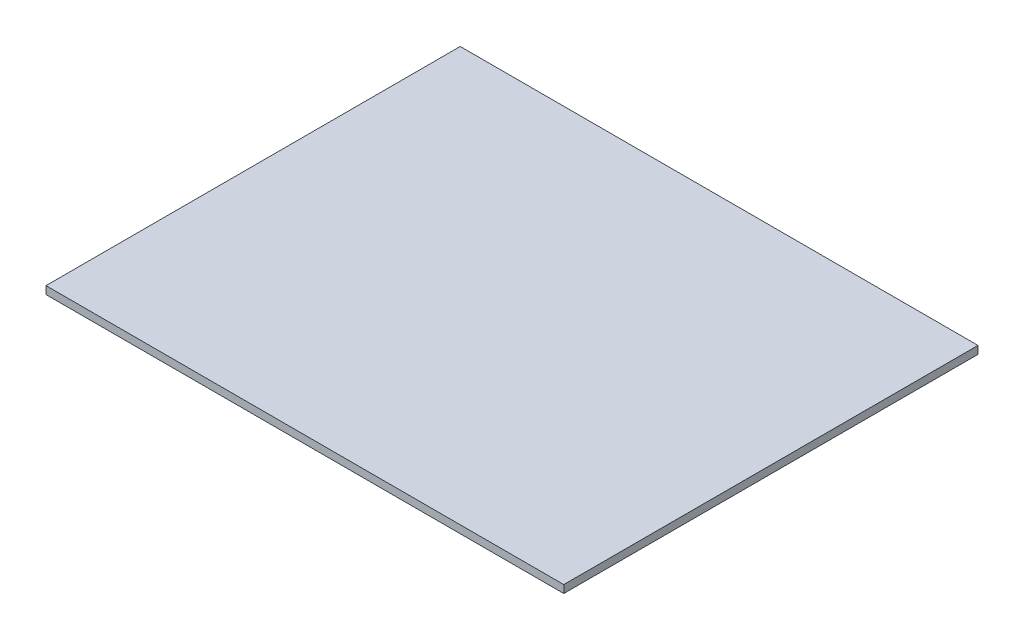
SolidWorks part; units mm, degrees
ref_plane "Front Plane" through (0, 0, 0) normal (0, 0, 1) x (1, 0, 0)
ref_plane "Top Plane" through (0, 0, 0) normal (0, 1, 0) x (1, 0, 0)
ref_plane "Right Plane" through (0, 0, 0) normal (1, 0, 0) x (0, 0, -1)
sketch "Sketch1" plane through (0, 0, 0) normal (0, 1, 0) x (1, 0, 0)
  line L1 (0, 0) -> (317.5, 0)
  line L2 (0, 0) -> (0, -254)
  line L3 (0, -254) -> (317.5, -254)
  line L4 (317.5, 0) -> (317.5, -254)
  dimension "D1" = 254
  dimension "D2" = 317.5
extrude "Boss-Extrude1" add sketch "Sketch1" along normal blind 4.7625 contours L1 L4 L3 L2
